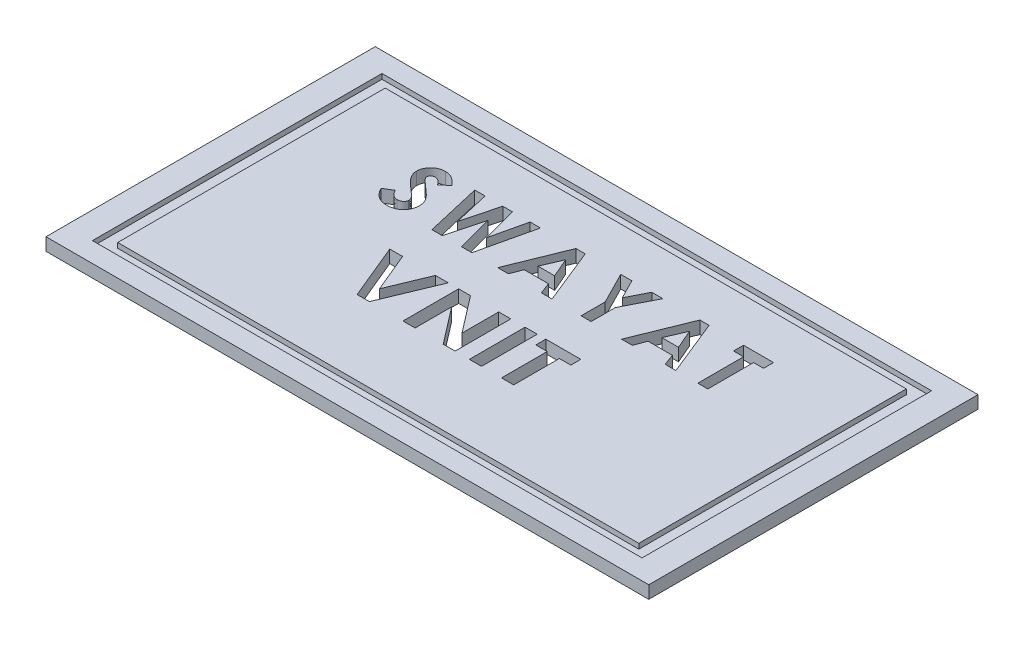
SolidWorks part; units mm, degrees
ref_plane "Front Plane" through (0, 0, 0) normal (0, 0, 1) x (1, 0, 0)
ref_plane "Top Plane" through (0, 0, 0) normal (0, 1, 0) x (1, 0, 0)
ref_plane "Right Plane" through (0, 0, 0) normal (1, 0, 0) x (0, 0, -1)
sketch "Sketch4" plane through (0, 0, 0) normal (0, 1, 0) x (1, 0, 0)
  line L1 (-59.5, -32.5) -> (59.5, -32.5)
  line L2 (-59.5, -32.5) -> (-59.5, 32.5)
  line L3 (-59.5, 32.5) -> (59.5, 32.5)
  line L4 (59.5, -32.5) -> (59.5, 32.5)
  line L5 (-59.5, -32.5) -> (59.5, 32.5) construction
  line L6 (-59.5, 32.5) -> (59.5, -32.5) construction
  point P0 (0, 0)
  dimension "D1" = 65
  dimension "D2" = 119
extrude "Boss-Extrude2" add sketch "Sketch4" along normal blind 2.5
sketch "Sketch5" plane through (0, 2.5, 0) normal (0, 1, 0) x (1, 0, 0)
  line L0 (-59.5, 6.8037) -> (59.5, 6.8037) construction
  line L1 (-59.5, 32.5) -> (-59.5, -32.5) construction
  line L2 (59.5, -32.5) -> (59.5, 32.5) construction
  line L3 (-59.5, -11.6706) -> (59.5, -11.6706) construction
  text T0 "<b>    SWAYAT</b>" font "Century Gothic" height 11
  text T1 "<b>       VNIT </b>" font "Century Gothic" height 11
extrude "Cut-Extrude1" cut sketch "Sketch5" against normal blind 2.5
sketch "Sketch6" plane through (0, 2.5, 0) normal (0, 1, 0) x (1, 0, 0)
  line L1 (-51.4356, -26.4019) -> (51.4356, -26.4019)
  line L2 (-51.4356, -26.4019) -> (-51.4356, 26.4019)
  line L3 (-51.4356, 26.4019) -> (51.4356, 26.4019)
  line L4 (51.4356, -26.4019) -> (51.4356, 26.4019)
  line L5 (-51.4356, -26.4019) -> (51.4356, 26.4019) construction
  line L6 (-51.4356, 26.4019) -> (51.4356, -26.4019) construction
  line L7 (-54.2519, -28.5795) -> (54.2519, -28.5795)
  line L8 (-54.2519, -28.5795) -> (-54.2519, 28.5795)
  line L9 (-54.2519, 28.5795) -> (54.2519, 28.5795)
  line L10 (54.2519, -28.5795) -> (54.2519, 28.5795)
  line L11 (-54.2519, -28.5795) -> (54.2519, 28.5795) construction
  line L12 (-54.2519, 28.5795) -> (54.2519, -28.5795) construction
  point P0 (0, 0)
  point P6 (0, 0)
extrude "Cut-Extrude2" cut sketch "Sketch6" against normal blind 1
